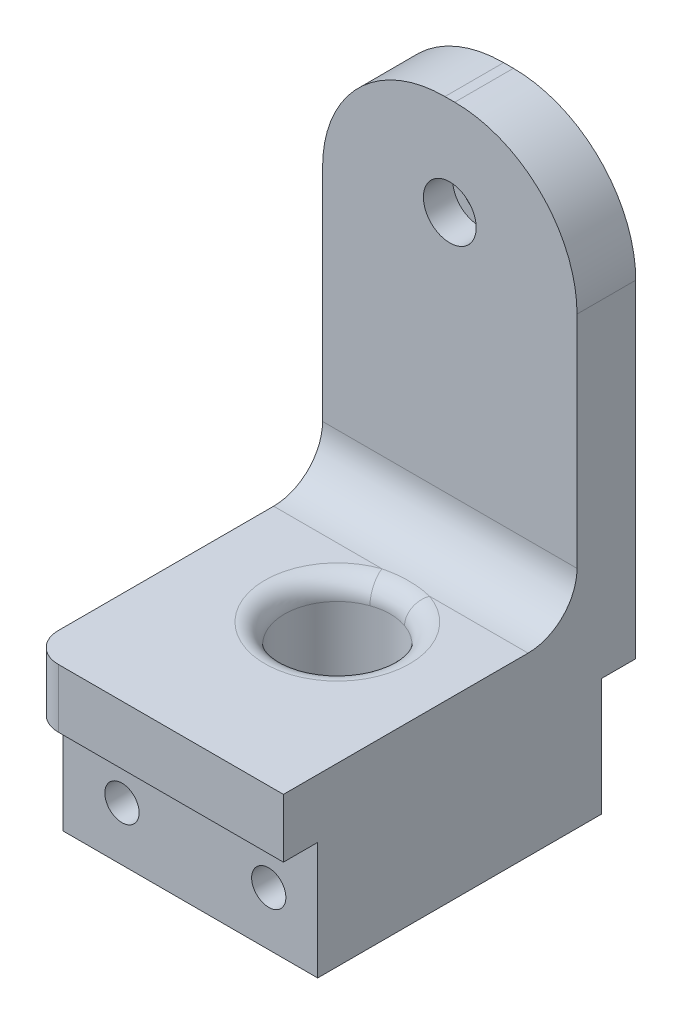
SolidWorks part; units mm, degrees
ref_plane "Front Plane" through (0, 0, 0) normal (0, 0, 1) x (1, 0, 0)
ref_plane "Top Plane" through (0, 0, 0) normal (0, 1, 0) x (1, 0, 0)
ref_plane "Right Plane" through (0, 0, 0) normal (1, 0, 0) x (0, 0, -1)
sketch "Sketch1" plane through (0, -44, 0) normal (0, 1, 0) x (1, 0, 0)
  line L0 (50.2641, 25) -> (50.2641, 28) construction
  line L1 (50.2641, -8) -> (50.2641, 28)
  line L2 (50.2641, -8) -> (27.2641, -8) construction
  line L3 (50.2641, -8) -> (27.2641, -8)
  line L4 (24.2641, -5) -> (24.2641, 25)
  line L5 (27.2641, 28) -> (50.2641, 28)
  arc A0 (27.2641, 28) -> (24.2641, 25) centre (27.2641, 25) ccw construction
  arc A1 (24.2641, -5) -> (27.2641, -8) centre (27.2641, -5) ccw construction
  arc A2 (27.2641, 28) -> (24.2641, 25) centre (27.2641, 25) ccw
  arc A3 (24.2641, -5) -> (27.2641, -8) centre (27.2641, -5) ccw
extrude "Boss-Extrude1" add sketch "Sketch1" along normal blind 6
sketch "Sketch2" plane through (0, -38, 0) normal (0, 1, 0) x (1, 0, 0)
  line L0 (24.2641, 25) -> (24.2641, -5) construction
  line L1 (50.2641, 28) -> (24.2641, 28)
  line L2 (50.2641, 28) -> (50.2641, 22)
  line L3 (50.2641, 22) -> (24.2641, 22)
  line L4 (24.2641, 28) -> (24.2641, 22)
  dimension "D1" = 6
extrude "Boss-Extrude2" add sketch "Sketch2" along normal blind 40
fillet "Fillet1" radius 12.5
sketch "Sketch3" plane through (0, 0, -22) normal (0, 0, 1) x (1, 0, 0)
  circle A0 centre (37.2641, -8) radius 2.7
extrude "Cut-Extrude1" cut sketch "Sketch3" against normal through all
sketch "Sketch4" plane through (0, -44, 0) normal (0, -1, 0) x (1, 0, 0)
  line L0 (24.2641, 5) -> (24.2641, -25) construction
  line L2 (24.2641, 4.5) -> (24.2641, -24.5)
  line L3 (50.2641, 4.5) -> (50.2641, -24.5)
  line L5 (24.2641, -25) -> (50.2641, -25) construction
  line L6 (50.2641, -24.5) -> (24.2641, -24.5)
  line L8 (24.2641, 4.5) -> (50.2641, 4.5)
  line L9 (50.2641, 5) -> (24.2641, 5) construction
  dimension "D1" = 0.5
  dimension "D2" = 0.5
extrude "Boss-Extrude3" add sketch "Sketch4" along normal blind 12
fillet "Fillet2" radius 5
sketch "Sketch5" plane through (0, 0, -24.5) normal (0, 0, -1) x (-1, 0, 0)
  circle A0 centre (-45.2641, -50.5) radius 1.75
  circle A1 centre (-30.2641, -50.5) radius 1.75
extrude "Cut-Extrude2" cut sketch "Sketch5" against normal through all
sketch "Sketch6" plane through (0, -38, 0) normal (0, -1, 0) x (1, 0, 0)
  line L2 (24.2641, -28) -> (27.2641, -28)
  line L3 (24.2641, -25) -> (24.2641, -28)
  line L4 (24.2641, -28) -> (27.2641, -28)
  line L5 (24.2641, -25) -> (24.2641, -28)
  arc A1 (24.2641, -25) -> (27.2641, -28) centre (27.2641, -25) ccw
  arc A2 (24.2641, -25) -> (27.2641, -28) centre (27.2641, -25) ccw
  dimension "D1" = 0
extrude "Cut-Extrude3" cut sketch "Sketch6" against normal through all
sketch "Sketch7" plane through (0, -56, 0) normal (0, -1, 0) x (1, 0, 0)
  line L0 (32.0141, 4.5) -> (28.5141, 4.5) construction
  line L1 (47.0141, 4.5) -> (43.5141, 4.5) construction
  line L2 (32.0141, 4.5) -> (28.5141, 4.5) construction
  line L3 (47.0141, 4.5) -> (43.5141, 4.5) construction
  line L4 (28.5141, 4.5) -> (28.5141, -10.0084) construction
  line L5 (47.0141, 4.5) -> (47.0141, -10.0084) construction
  line L6 (28.5141, -10.0084) -> (47.0141, -10.0084) construction
  circle A0 centre (37.7641, -10.0084) radius 5.4
extrude "Cut-Extrude4" cut sketch "Sketch7" against normal up to surface (18 mm away)
fillet "Fillet3" radius 2
sketch "Sketch8" plane through (0, 0, -28) normal (0, 0, -1) x (-1, 0, 0)
  circle A0 centre (-37.2641, -8) radius 2.7 construction
  circle A1 centre (-37.2641, -8) radius 2.7
  circle A2 centre (-37.2641, -8) radius 1.6
extrude "Boss-Extrude4" add sketch "Sketch8" against normal blind 3
